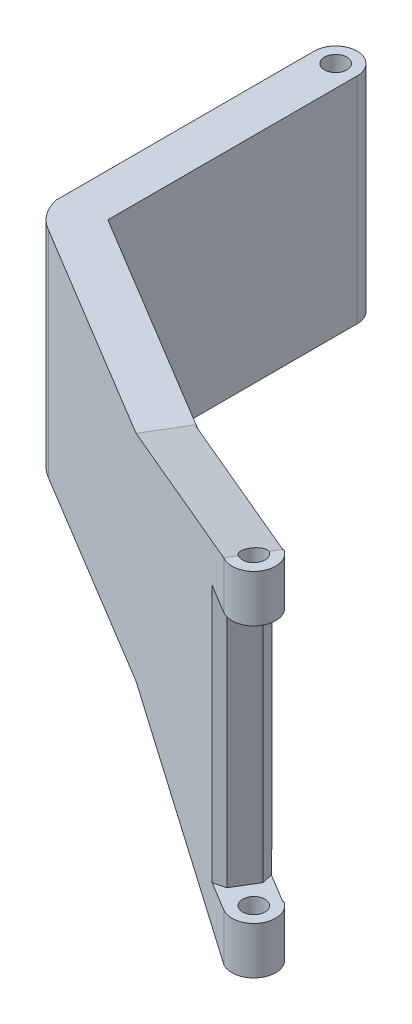
SolidWorks part; units mm, degrees
ref_plane "前视基准面" through (0, 0, 0) normal (0, 0, 1) x (1, 0, 0)
ref_plane "上视基准面" through (0, 0, 0) normal (0, 1, 0) x (1, 0, 0)
ref_plane "右视基准面" through (0, 0, 0) normal (1, 0, 0) x (0, 0, -1)
sketch "草图1" plane through (0, 0, 0) normal (0, 1, 0) x (1, 0, 0)
  circle A2 centre (0, 0) radius 1.3
  circle A3 centre (0, 0) radius 2.5
extrude "凸台-拉伸1" add sketch "草图1" along normal blind 25 contours A2
sketch "草图2" plane through (0, 25, 0) normal (0, 1, 0) x (1, 0, 0)
  line L0 (-2.5, 0) -> (-2.5, -30)
  line L1 (2.5, 0) -> (2.5, -29.0257)
  line L2 (2.5, -29.0257) -> (53.9615, -60)
  line L3 (53.9615, -60) -> (51.3357, -64.3626)
  line L4 (2.5, -29.0257) -> (-0.1258, -33.3884)
  line L5 (51.3357, -64.3626) -> (-0.1258, -33.3884)
  circle A0 centre (0, 0) radius 2.5 construction
  arc A1 (-2.5, -30) -> (0, -33.4641) centre (2.5, -29.0257) ccw
  circle M2 centre (0, 0) radius 2.5
extrude "凸台-拉伸2" add sketch "草图2" against normal blind 25 contours L0 A1 L4 L1 M2 | L5 L3 L2 L4
sketch "草图3" plane through (0, 25, 0) normal (0, 1, 0) x (1, 0, 0)
  line L0 (53.9615, -60) -> (51.3357, -64.3626) construction
  line L1 (53.9615, -60) -> (51.3357, -64.3626)
  arc A0 (53.9615, -60) -> (51.3357, -64.3626) centre (52.6486, -62.1813) cw
extrude "凸台-拉伸3" add sketch "草图3" against normal blind 33 and the other way blind 8 contours A0 L1
sketch "草图5" plane through (-14.7854, 0, 24.5649) normal (-0.5157, 0, 0.8568) x (0.8568, 0, 0.5157)
  line L0 (77.1742, 25) -> (77.1742, 33)
  line L1 (77.1742, 33) -> (47.2156, 25)
  line L2 (77.1742, 25) -> (17.257, 25) construction
  line L3 (47.2156, 25) -> (77.1742, 25)
extrude "凸台-拉伸4" add sketch "草图5" against normal blind 5
sketch "草图4" plane through (0, 25, 0) normal (0, 1, 0) x (1, 0, 0)
  circle A0 centre (52.6486, -62.1813) radius 1.3
sketch "草图6" plane through (-14.7854, 0, 24.5649) normal (-0.5157, 0, 0.8568) x (0.8568, 0, 0.5157)
  line L0 (17.257, 12.5) -> (76.7841, 12.5)
  line L1 (17.257, 0) -> (17.257, 25) construction
ref_plane "基准面1" through (0, 12.5, 0) normal (0, -1, 0) x (0.8568, 0, 0.5157)
mirror "镜向1" about plane through (0, 12.5, 0) normal (0, -1, 0) of "凸台-拉伸4"
extrude "切除-拉伸1" cut sketch "草图4" against normal through all both and the other way through all contours A0
sketch "草图7" plane through (-14.7854, 0, 24.5649) normal (-0.5157, 0, 0.8568) x (0.8568, 0, 0.5157)
  line L0 (77.1742, -2.5) -> (77.1742, 27.5)
  line L1 (77.1742, -8) -> (77.1742, 33) construction
  line L2 (-39.9312, 12.5) -> (39.9312, 12.5) construction
  line L3 (77.1742, 27.5) -> (79.7202, 27.5)
  line L4 (79.7202, -8) -> (79.7202, 33) construction
  line L5 (79.7202, 27.5) -> (79.7202, -2.5)
  line L6 (79.7202, -2.5) -> (77.1742, -2.5)
  line L7 (77.1742, 27.5) -> (74.1742, 27.5)
  line L8 (74.1742, 27.5) -> (74.1742, -2.5)
  line L9 (74.1742, -2.5) -> (77.1742, -2.5)
  point P5 (77.1742, 12.5)
  point P13 (77.1742, -2.556)
  line M2 (77.1742, -8) -> (77.1742, 33)
extrude "切除-拉伸2" cut sketch "草图7" against normal blind 9 and the other way through all contours L8 L9 L7 M2 | L6 L5 L3 M2
chamfer "倒角1" distance 1 angle 45 2 edges at (48.7654, 12.5, 62.8156) (51.3912, 12.5, 58.4529)
